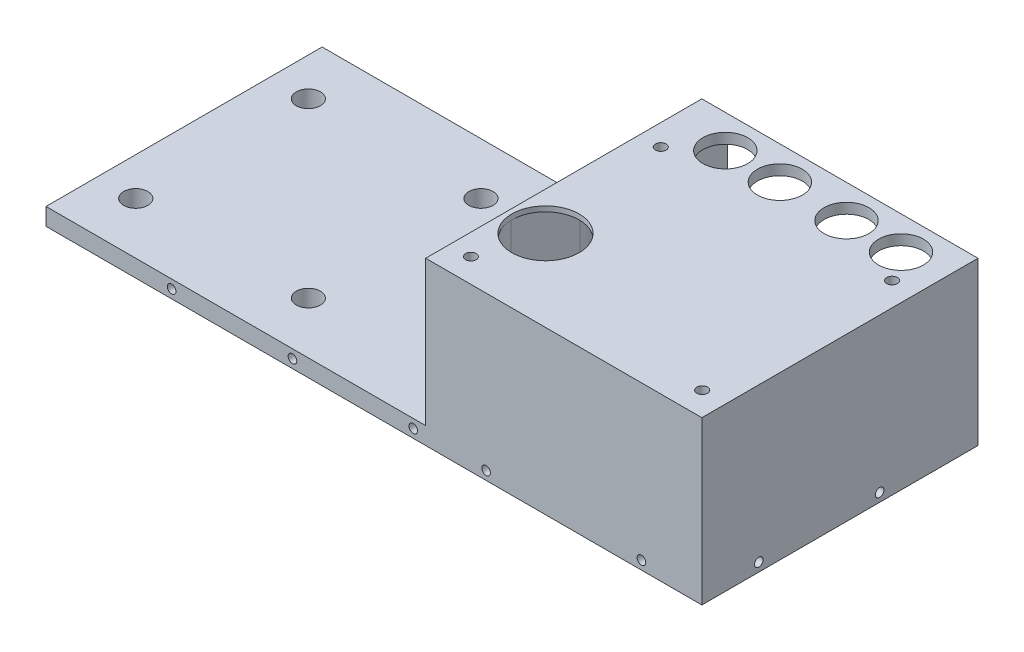
SolidWorks part; units mm, degrees
ref_plane "Front Plane" through (0, 0, 0) normal (0, 0, 1) x (1, 0, 0)
ref_plane "Top Plane" through (0, 0, 0) normal (0, 1, 0) x (1, 0, 0)
ref_plane "Right Plane" through (0, 0, 0) normal (1, 0, 0) x (0, 0, -1)
sketch "Sketch1" plane through (0, 0, 0) normal (0, 1, 0) x (1, 0, 0)
  line L1 (-95, 40) -> (95, 40)
  line L2 (-95, 40) -> (-95, -40)
  line L3 (-95, -40) -> (95, -40)
  line L4 (95, 40) -> (95, -40)
  line L5 (-95, 40) -> (95, -40) construction
  line L6 (-95, -40) -> (95, 40) construction
  point P0 (0, 0)
  dimension "D1" = 80
  dimension "D2" = 190
extrude "Boss-Extrude1" add sketch "Sketch1" along normal blind 5
sketch "Sketch3" plane through (0, 5, 0) normal (0, 1, 0) x (1, 0, 0)
  line L0 (-95, -40) -> (95, -40) construction
  line L1 (95, 40) -> (15, 40)
  line L2 (95, 40) -> (95, -40)
  line L3 (95, -40) -> (15, -40)
  line L4 (15, 40) -> (15, -40)
extrude "Boss-Extrude2" add sketch "Sketch3" along normal blind 42
sketch "Sketch5" plane through (0, 0, 0) normal (0, -1, 0) x (1, 0, 0)
  line L0 (31.4, -30.4) -> (82.3, -30.4) construction
  line L1 (95, 40) -> (95, -40) construction
  line L2 (95, -40) -> (-95, -40) construction
  circle A0 centre (31.4, -30.4) radius 6.5
  circle A1 centre (47.2, -30.4) radius 6.5
  circle A2 centre (66.5, -30.4) radius 6.5
  circle A3 centre (82.3, -30.4) radius 6.5
  dimension "D1" = 13
  dimension "D2" = 15.8
  dimension "D3" = 15.8
  dimension "D4" = 19.3
  dimension "D5" = 12.7
  dimension "D6" = 9.6
extrude "Cut-Extrude2" cut sketch "Sketch5" against normal through all
sketch "Sketch6" plane through (0, 0, 0) normal (0, -1, 0) x (1, 0, 0)
  line L0 (31.4, -21.4) -> (82.3, -21.4)
  line L1 (82.3, -39.4) -> (31.4, -39.4)
  arc A0 (82.3, -21.4) -> (82.3, -39.4) centre (82.3, -30.4) cw
  arc A1 (31.4, -39.4) -> (31.4, -21.4) centre (31.4, -30.4) cw
  circle A2 centre (31.4, -30.4) radius 6.5 construction
  circle A3 centre (82.3, -30.4) radius 6.5 construction
  dimension "D1" = 9
extrude "Cut-Extrude3" cut sketch "Sketch6" against normal offset from surface (44 mm away) 3 up to face at (31.4, 47, -36.9)
sketch "Sketch7" plane through (0, 0, 0) normal (0, -1, 0) x (1, 0, 0)
  line L0 (-84, 0) -> (-95, 0) construction
  line L1 (-84, 25) -> (-34, 25) construction
  line L2 (-84, 25) -> (-84, -25) construction
  line L3 (-84, -25) -> (-34, -25) construction
  line L4 (-34, 25) -> (-34, -25) construction
  line L5 (-95, -40) -> (-95, 40) construction
  circle A0 centre (-84, 25) radius 3.5
  circle A1 centre (-34, 25) radius 3.5
  circle A2 centre (-84, -25) radius 3.5
  circle A3 centre (-34, -25) radius 3.5
  dimension "D1" = 7
  dimension "D2" = 50
  dimension "D3" = 11
extrude "Cut-Extrude4" cut sketch "Sketch7" against normal through all
sketch "Sketch8" plane through (0, 0, 0) normal (0, -1, 0) x (1, 0, 0)
  circle A0 centre (26.1, 16.4) radius 9.75
  circle A2 centre (31.4, -30.4) radius 6.5 construction
  dimension "D1" = 5.3
  dimension "D2" = 46.8
  dimension "D3" = 19.5
extrude "Cut-Extrude5" cut sketch "Sketch8" against normal through all
sketch "Sketch4" plane through (0, 47, 0) normal (0, 1, 0) x (1, 0, 0)
  line L1 (21.15, 21.95) -> (88.15, 21.95) construction
  line L2 (21.15, 21.95) -> (21.15, -33.05) construction
  line L3 (21.15, -33.05) -> (88.15, -33.05) construction
  line L4 (88.15, 21.95) -> (88.15, -33.05) construction
  circle A0 centre (21.15, 21.95) radius 1.55
  circle A1 centre (88.15, 21.95) radius 1.55
  circle A2 centre (21.15, -33.05) radius 1.55
  circle A3 centre (88.15, -33.05) radius 1.55
  circle A4 centre (31.4, 30.4) radius 6.5 construction
  dimension "D1" = 3.1
  dimension "D4" = 8.45
  dimension "D5" = 10.25
  dimension "D2" = 55
  dimension "D3" = 67
extrude "Cut-Extrude1" cut sketch "Sketch4" against normal through all
sketch "Sketch9" plane through (0, 0, 0) normal (0, -1, 0) x (1, 0, 0)
  circle A0 centre (21.15, -21.95) radius 3.5
  circle A1 centre (88.15, -21.95) radius 3.5
  circle A2 centre (21.15, 33.05) radius 3.5
  circle A3 centre (88.15, 33.05) radius 3.5
  dimension "D1" = 7
extrude "Cut-Extrude6" cut sketch "Sketch9" against normal offset from surface (44 mm away) 3 up to face at (88.15, 47, -20.4)
sketch "Sketch10" plane through (0, 0, 0) normal (0, -1, 0) x (1, 0, 0)
  circle A0 centre (26.1, 16.4) radius 10
  dimension "D1" = 20
extrude "Cut-Extrude7" cut sketch "Sketch10" against normal offset from surface (45.5 mm away) 1.5 up to face at (88.15, 47, -20.4)
sketch "Sketch13" plane through (0, 0, -40) normal (0, 0, -1) x (-1, 0, 0)
  line L0 (-11.4, 2.5) -> (23.6, 2.5) construction
  line L1 (23.6, 2.5) -> (58.6, 2.5) construction
  line L2 (-11.4, 0) -> (-11.4, 2.5) construction
  line L3 (-95, 0) -> (95, 0) construction
  line L4 (-11.4, 2.5) -> (-11.4, 5) construction
  line L5 (-15, 5) -> (95, 5) construction
  circle A0 centre (-11.4, 2.5) radius 1.5
  circle A1 centre (23.6, 2.5) radius 1.5
  circle A2 centre (58.6, 2.5) radius 1.5
  dimension "D1" = 3
  dimension "D2" = 35
  dimension "D3" = 20
hole_wizard "M3 Tapped Hole1" positions "3DSketch1" profile "Sketch15" tap size "M3" standard "IS"
sketch3d "3DSketch1"
  point P0 (11.4, 2.5, -40)
  point P3 (-23.6, 2.5, -40)
  point P6 (-58.6, 2.5, -40)
sketch "Sketch15" plane through (11.4, 2.5, -40) normal (1, 0, 0) x (0, 1, 0)
  line L0 (0, 0) -> (0, 9.2511)
  line L1 (0, 9.2511) -> (1.25, 8.5)
  line L2 (1.25, 8.5) -> (1.25, 0)
  line L5 (1.25, 0) -> (0, 0)
  line L10 (0, 9.2511) -> (-1.25, 8.5) construction
  line L11 (0, -6.35) -> (0, 107.95) construction
  dimension "Tap Drill Dia." = 2.5
  dimension "Tap Drill Depth" = 8.5
  dimension "Drill Angle" = 118
cosmetic thread "Hole Thread1" parameters "D1"=6, "D2"=3
cosmetic thread "Hole Thread2" parameters "D1"=6, "D2"=3
cosmetic thread "Hole Thread3" parameters "D1"=6, "D2"=3
mirror "Mirror1" about plane through (0, 0, 0) normal (0, 0, 1) of "M3 Tapped Hole1"
sketch "Sketch16" plane through (0, 0, 40) normal (0, 0, 1) x (1, 0, 0)
  line L0 (32.5, 2.5) -> (77.5, 2.5) construction
  line L1 (11.4, 2.5) -> (-23.6, 2.5) construction
  line L2 (55, 2.5) -> (55, 47) construction
  line L3 (15, 47) -> (95, 47) construction
  point P0 (32.5, 2.5)
  point P1 (77.5, 2.5)
  dimension "D1" = 45
hole_wizard "M3 Tapped Hole2" positions "3DSketch3" profile "Sketch18" tap size "M3" standard "IS"
sketch3d "3DSketch3"
  point P0 (32.5, 2.5, 40)
  point P3 (77.5, 2.5, 40)
sketch "Sketch18" plane through (32.5, 2.5, 40) normal (1, 0, 0) x (0, -1, 0)
  line L0 (0, 0) -> (0, 8.2511)
  line L1 (0, 8.2511) -> (1.25, 7.5)
  line L2 (1.25, 7.5) -> (1.25, 0)
  line L5 (1.25, 0) -> (0, 0)
  line L10 (0, 8.2511) -> (-1.25, 7.5) construction
  line L11 (0, -6.35) -> (0, 107.95) construction
  dimension "Tap Drill Dia." = 2.5
  dimension "Tap Drill Depth" = 7.5
  dimension "Drill Angle" = 118
cosmetic thread "Hole Thread4" parameters "D1"=6, "D2"=3
cosmetic thread "Hole Thread5" parameters "D1"=6, "D2"=3
sketch "Sketch19" plane through (95, 0, 0) normal (1, 0, 0) x (0, 0, -1)
  line L0 (-23.5, 2.5) -> (11.5, 2.5) construction
  line L1 (-40, 47) -> (-40, 0) construction
  point P0 (-23.5, 2.5)
  point P1 (11.5, 2.5)
  dimension "D1" = 35
  dimension "D2" = 16.5
hole_wizard "M3 Tapped Hole3" positions "3DSketch4" profile "Sketch20" tap size "M3" standard "IS"
sketch3d "3DSketch4"
  point P0 (95, 2.5, 23.5)
  point P3 (95, 2.5, -11.5)
sketch "Sketch20" plane through (95, 2.5, 23.5) normal (0, 1, 0) x (0, 0, -1)
  line L0 (0, 0) -> (0, 8.2511)
  line L1 (0, 8.2511) -> (1.25, 7.5)
  line L2 (1.25, 7.5) -> (1.25, 0)
  line L5 (1.25, 0) -> (0, 0)
  line L10 (0, 8.2511) -> (-1.25, 7.5) construction
  line L11 (0, -6.35) -> (0, 107.95) construction
  dimension "Tap Drill Dia." = 2.5
  dimension "Tap Drill Depth" = 7.5
  dimension "Drill Angle" = 118
cosmetic thread "Hole Thread6" parameters "D1"=6, "D2"=3
cosmetic thread "Hole Thread7" parameters "D1"=6, "D2"=3
sketch "Sketch21" plane through (0, 0, 0) normal (0, -1, 0) x (1, 0, 0)
  line L0 (16.1, 16.4) -> (26.1, 16.4)
  line L1 (26.1, 16.4) -> (26.1, 26.4)
  line L2 (26.1, 26.4) -> (51.1, 26.4)
  line L3 (51.1, 26.4) -> (51.1, -8.6)
  line L4 (51.1, -8.6) -> (16.1, -8.6)
  line L5 (16.1, -8.6) -> (16.1, 16.4)
  circle A0 centre (26.1, 16.4) radius 10 construction
  circle A1 centre (26.1, 16.4) radius 10 construction
  circle A2 centre (26.1, 16.4) radius 9.75 construction
  dimension "D1" = 35
extrude "Cut-Extrude8" cut sketch "Sketch21" against normal up to surface (45.5 mm away) up to face at (26.1, 45.5, 6.4)
fillet "Fillet1" radius 5 3 edges at (51.1, 22.75, 26.4) (51.1, 22.75, -8.6) (16.1, 22.75, -8.6)
sketch "草图1" plane through (0, 0, 0) normal (0, -1, 0) x (1, 0, 0)
  line L0 (95, -40) -> (-95, -40) construction
  line L1 (22.4, -30.4) -> (91.3, -30.4)
  line L2 (22.4, -30.4) -> (22.4, -40)
  line L3 (22.4, -40) -> (91.3, -40)
  line L4 (91.3, -30.4) -> (91.3, -40)
  arc A0 (31.4, -21.4) -> (31.4, -39.4) centre (31.4, -30.4) ccw construction
  arc A1 (82.3, -39.4) -> (89.5998, -25.1356) centre (82.3, -30.4) ccw construction
extrude "切除-拉伸1" cut sketch "草图1" against normal up to surface (44 mm away) up to face at (88.15, 44, -23.5)
